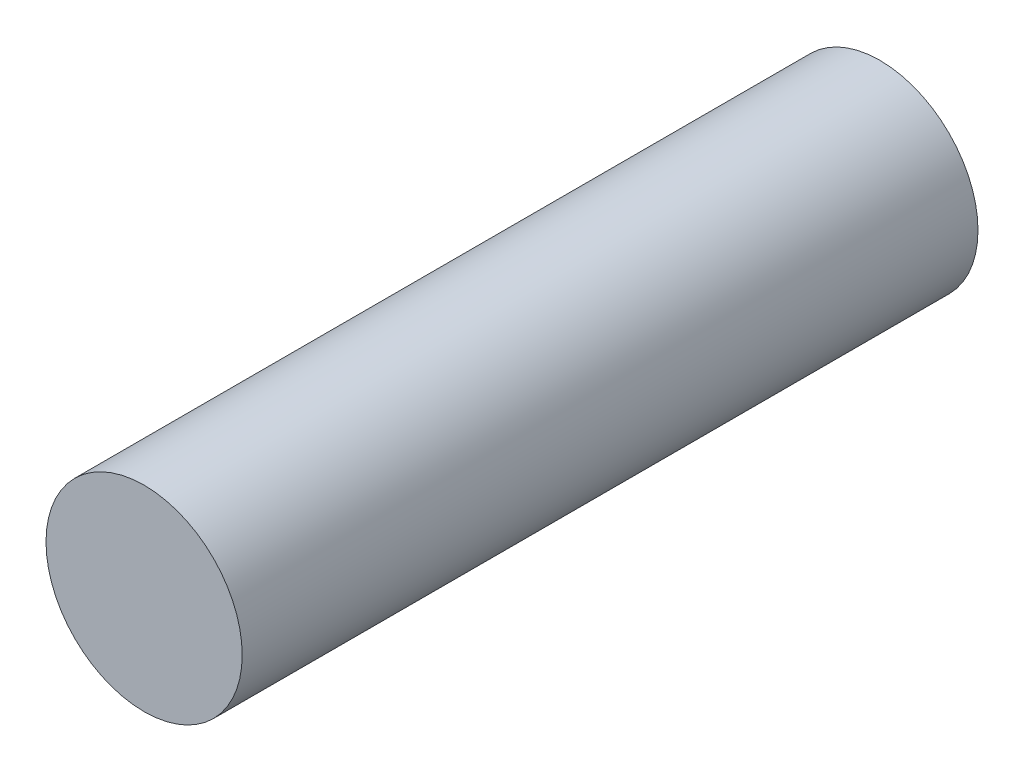
SolidWorks part; units mm, degrees
material "AISI 304"
ref_plane "Front Plane" through (0, 0, 0) normal (0, 0, 1) x (1, 0, 0)
ref_plane "Top Plane" through (0, 0, 0) normal (0, 1, 0) x (1, 0, 0)
ref_plane "Right Plane" through (0, 0, 0) normal (1, 0, 0) x (0, 0, -1)
sketch "Sketch1" plane through (0, 0, 0) normal (0, 0, 1) x (1, 0, 0)
  circle A0 centre (0, 0) radius 2
  dimension "D1" = 4
extrude "Boss-Extrude1" add sketch "Sketch1" along normal blind 15
